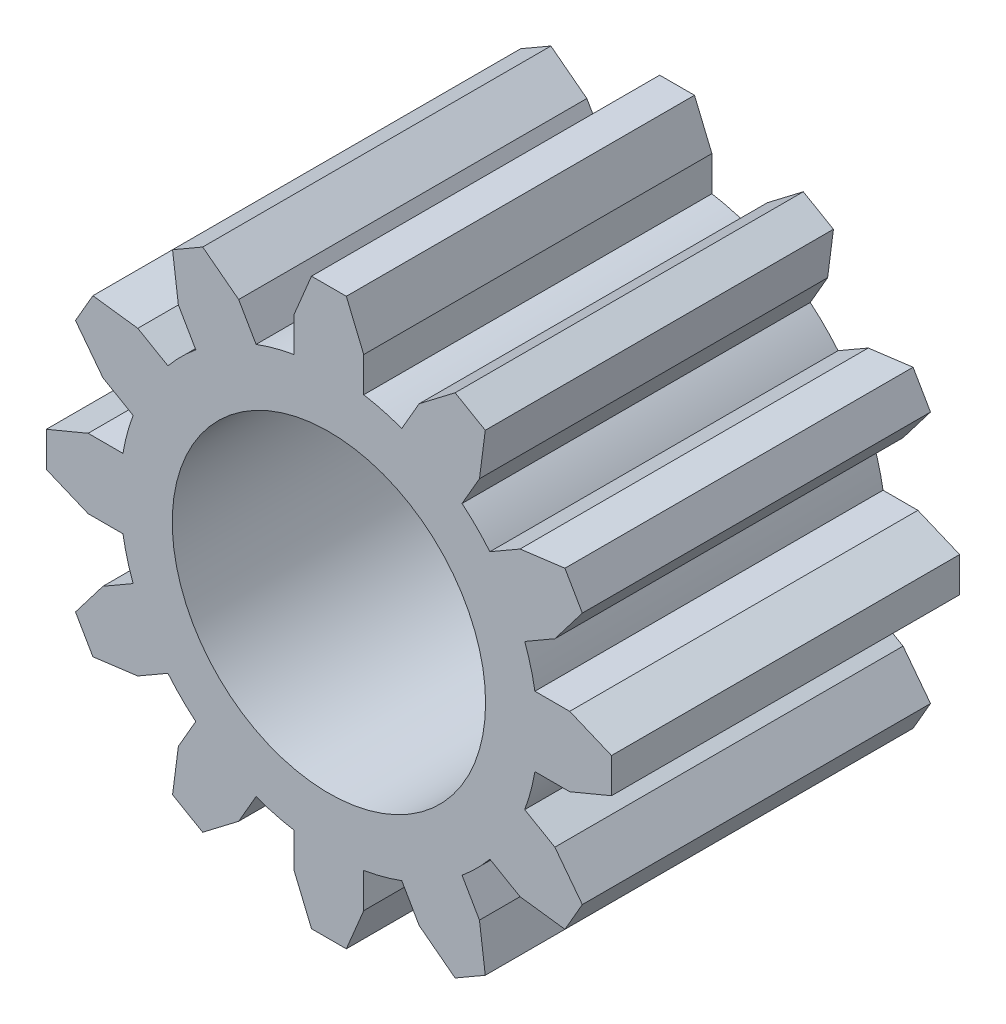
SolidWorks part; units mm, degrees
ref_plane "Front Plane" through (0, 0, 0) normal (0, 0, 1) x (1, 0, 0)
ref_plane "Top Plane" through (0, 0, 0) normal (0, 1, 0) x (1, 0, 0)
ref_plane "Right Plane" through (0, 0, 0) normal (1, 0, 0) x (0, 0, -1)
sketch "Sketch1" plane through (0, 0, 0) normal (0, 0, 1) x (1, 0, 0)
  line L0 (0, 0) -> (0, 8.1161) construction
  line L1 (-1, 5.9161) -> (-1, 6.9161)
  line L2 (-1, 6.9161) -> (-0.5, 8.1161)
  line L3 (-0.5, 8.1161) -> (0.5, 8.1161)
  line L4 (0.5, 8.1161) -> (1, 6.9161)
  line L5 (1, 6.9161) -> (1, 5.9161)
  circle A0 centre (0, 0) radius 4.5
  circle A1 centre (0, 0) radius 6
  point P7 (0, 0)
  point P13 (0, 0)
  dimension "D1" = 9
  dimension "D2" = 12
  dimension "D3" = 1
  dimension "D4" = 1
  dimension "D5" = 0.5
  dimension "D6" = 0.5
  dimension "D7" = 1
  dimension "D8" = 1
  dimension "D9" = 1.2
extrude "Boss-Extrude1" add sketch "Sketch1" along normal mid plane 10
pattern_circular "CirPattern1" count 12 over 360 about axis through (0, 0, 0) along (0, 0, 1) of "Boss-Extrude1"
sketch "Sketch2" plane through (0, 0, 5) normal (0, 0, 1) x (1, 0, 0)
  point P0 (0, 0)
